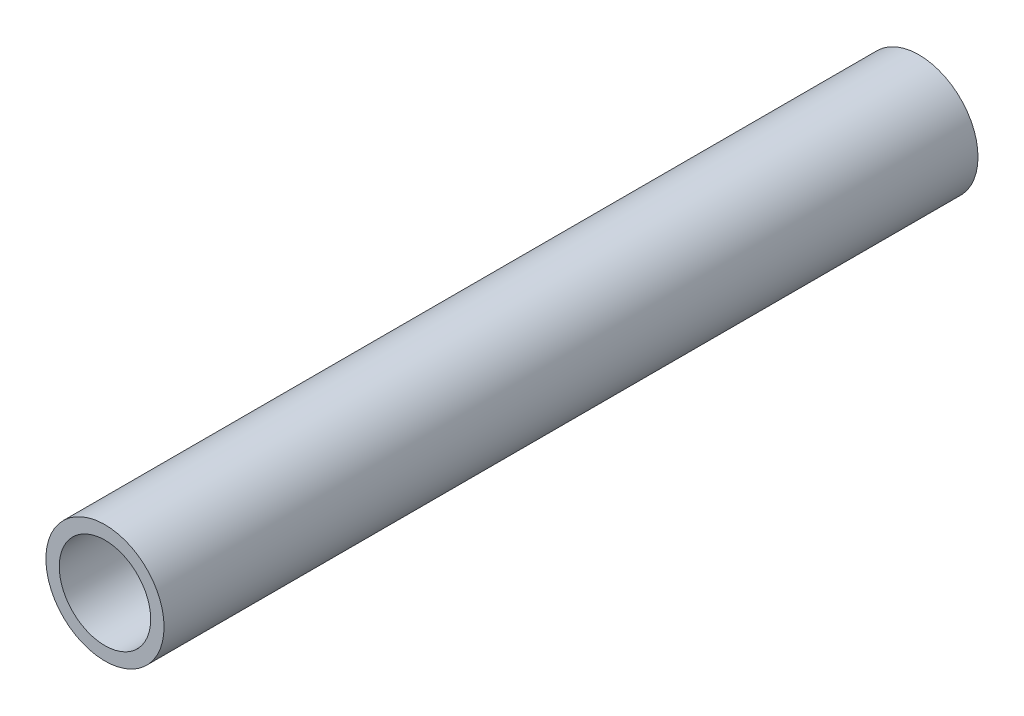
SolidWorks part; units mm, degrees
ref_plane "Front Plane" through (0, 0, 0) normal (0, 0, 1) x (1, 0, 0)
ref_plane "Top Plane" through (0, 0, 0) normal (0, 1, 0) x (1, 0, 0)
ref_plane "Right Plane" through (0, 0, 0) normal (1, 0, 0) x (0, 0, -1)
sketch "Sketch1" plane through (0, 0, 0) normal (0, 0, 1) x (1, 0, 0)
  circle A0 centre (0, 0) radius 3.425
  circle A1 centre (0, 0) radius 4.425
  dimension "D1" = 6.85
  dimension "D2" = 1
extrude "Boss-Extrude1" add sketch "Sketch1" along normal blind 60.96
